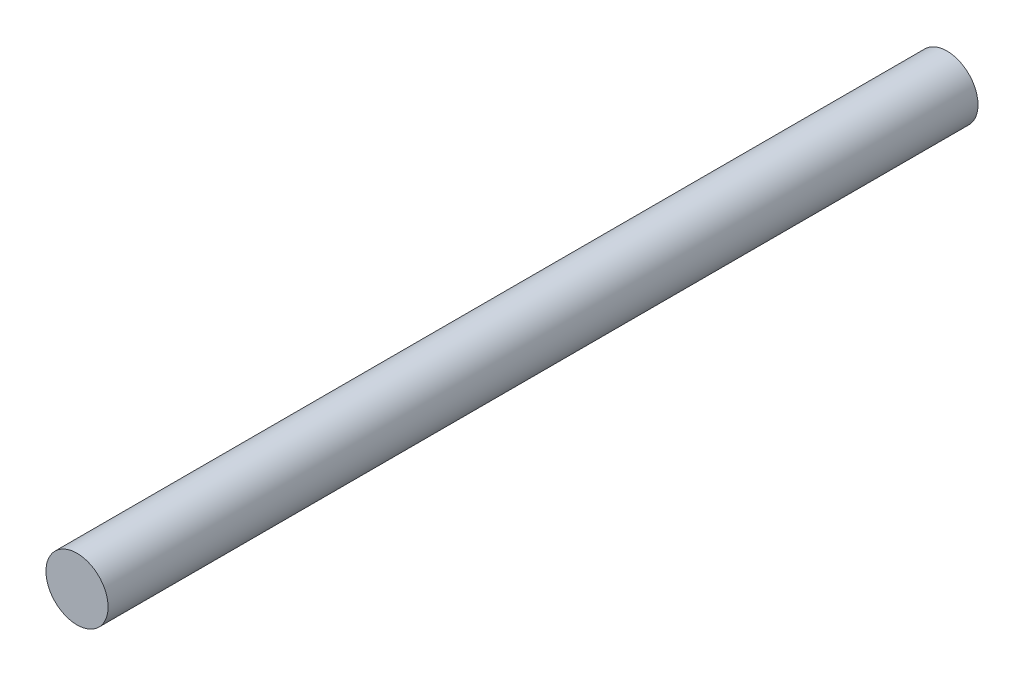
SolidWorks part; units mm, degrees
ref_plane "Front Plane" through (0, 0, 0) normal (0, 0, 1) x (1, 0, 0)
ref_plane "Top Plane" through (0, 0, 0) normal (0, 1, 0) x (1, 0, 0)
ref_plane "Right Plane" through (0, 0, 0) normal (1, 0, 0) x (0, 0, -1)
sketch "Sketch1" plane through (0, 0, 0) normal (0, 0, 1) x (1, 0, 0)
  circle A0 centre (0, 0) radius 2.5
  dimension "D1" = 5
extrude "Boss-Extrude1" add sketch "Sketch1" along normal blind 70
